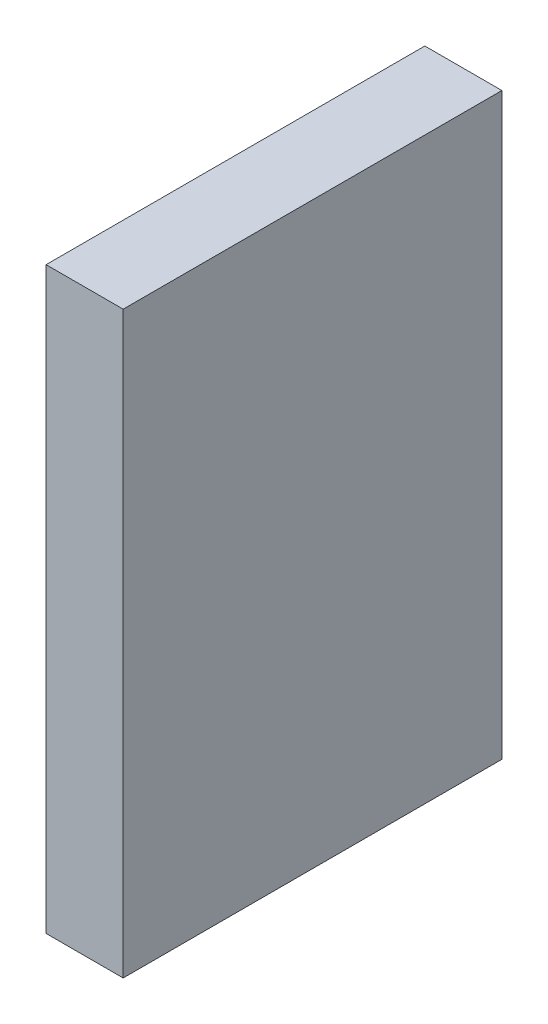
SolidWorks part; units mm, degrees
ref_plane "Front Plane" through (0, 0, 0) normal (0, 0, 1) x (1, 0, 0)
ref_plane "Top Plane" through (0, 0, 0) normal (0, 1, 0) x (1, 0, 0)
ref_plane "Right Plane" through (0, 0, 0) normal (1, 0, 0) x (0, 0, -1)
sketch "Sketch1" plane through (0, 0, 0) normal (1, 0, 0) x (0, 0, -1)
  line L1 (-101.1445, 211.455) -> (114.7555, 211.455)
  line L2 (-101.1445, 211.455) -> (-101.1445, -118.745)
  line L3 (-101.1445, -118.745) -> (114.7555, -118.745)
  line L4 (114.7555, 211.455) -> (114.7555, -118.745)
  dimension "D1" = 215.9
  dimension "D2" = 330.2
extrude "Boss-Extrude1" add sketch "Sketch1" along normal blind 43.942
